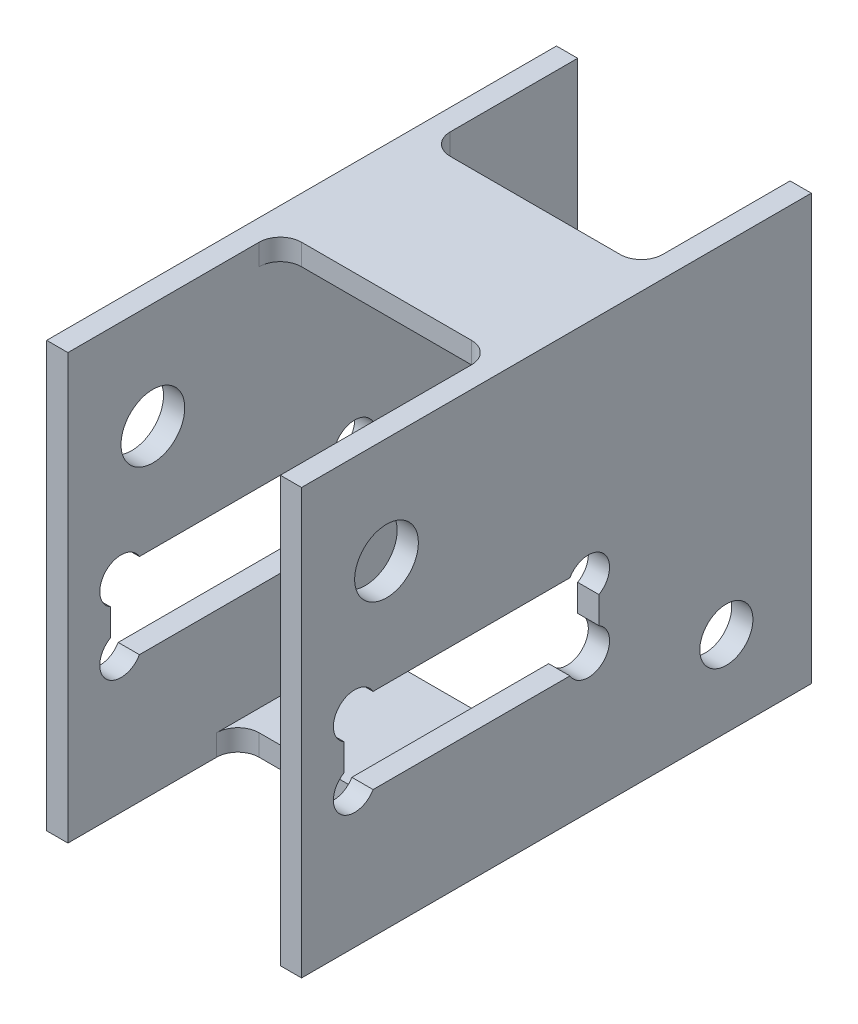
SolidWorks part; units mm, degrees
material "6061 Alloy"
ref_plane "Front Plane" through (0, 0, 0) normal (0, 0, 1) x (1, 0, 0)
ref_plane "Top Plane" through (0, 0, 0) normal (0, 1, 0) x (1, 0, 0)
ref_plane "Right Plane" through (0, 0, 0) normal (1, 0, 0) x (0, 0, -1)
sketch "Sketch1" plane through (0, 0, 0) normal (0, 0, 1) x (1, 0, 0)
  line L1 (-19.05, -31.75) -> (19.05, -31.75)
  line L2 (-19.05, -31.75) -> (-19.05, 31.75)
  line L3 (-19.05, 31.75) -> (19.05, 31.75)
  line L4 (19.05, -31.75) -> (19.05, 31.75)
  line L5 (-19.05, -31.75) -> (19.05, 31.75) construction
  line L6 (-19.05, 31.75) -> (19.05, -31.75) construction
  line L7 (-15.875, -28.575) -> (15.875, -28.575)
  line L8 (-15.875, -28.575) -> (-15.875, 28.575)
  line L9 (-15.875, 28.575) -> (15.875, 28.575)
  line L10 (15.875, -28.575) -> (15.875, 28.575)
  line L11 (-15.875, -28.575) -> (15.875, 28.575) construction
  line L12 (-15.875, 28.575) -> (15.875, -28.575) construction
  point P0 (0, 0)
  point P6 (0, 0)
  dimension "D1" = 63.5
  dimension "D2" = 38.1
  dimension "D3" = 3.175
  dimension "D4" = 3.175
extrude "Boss-Extrude1" add sketch "Sketch1" along normal blind 76.2
sketch "Sketch2" plane through (19.05, 0, 0) normal (1, 0, 0) x (0, 0, -1)
  line L0 (-76.2, -31.75) -> (-76.2, 31.75) construction
  line L1 (-76.2, 31.75) -> (0, 31.75) construction
  line L2 (-50.8, -4.0293) -> (-50.8, -9.0888) construction
  line L3 (-69.85, -12.7) -> (-31.75, -12.7)
  line L4 (-69.85, -12.7) -> (-69.85, 0)
  line L5 (-69.85, 0) -> (-31.75, 0)
  line L6 (-31.75, -12.7) -> (-31.75, 0)
  line L7 (-69.85, -12.7) -> (-31.75, 0) construction
  line L8 (-69.85, 0) -> (-31.75, -12.7) construction
  circle A0 centre (-63.5, 15.875) radius 4.7625
  circle A1 centre (-12.7, -19.05) radius 3.9688
  circle A3 centre (-68.2625, -1.5875) radius 3.175
  circle A4 centre (-68.2625, -11.1125) radius 3.175
  circle A5 centre (-33.3375, -11.1125) radius 3.175
  circle A6 centre (-33.3375, -1.5875) radius 3.175
  point P6 (-50.8, -6.35)
  dimension "D1" = 9.525
  dimension "D10" = 7.9375
  dimension "D11" = 6.35
  dimension "D12" = 1.5875
  dimension "D2" = 12.7
  dimension "D3" = 15.875
  dimension "D4" = 38.1
  dimension "D5" = 12.7
  dimension "D6" = 6.35
  dimension "D7" = 15.875
  dimension "D8" = 50.8
  dimension "D9" = 34.925
  dimension "D13" = 1.5875
  dimension "D14" = 1.5875
extrude "Cut-Extrude1" cut sketch "Sketch2" against normal through all contours L6 A6 L5 A3 L4 A4 L3 A5 | L4 A3 L5 | L5 A3 L4 | A6 L6 L5 | A6 L5 L6 | A5 L6 L3 | A5 L3 L6 | L3 A4 L4 | L4 A4 L3 | A0 | A1
sketch "Sketch3" plane through (0, 31.75, 0) normal (0, 1, 0) x (1, 0, 0)
  line L0 (19.05, -76.2) -> (-19.05, -76.2) construction
  line L1 (-15.875, -44.45) -> (15.875, -44.45)
  line L2 (-15.875, -44.45) -> (-15.875, -76.2)
  line L3 (-15.875, -76.2) -> (15.875, -76.2)
  line L4 (15.875, -44.45) -> (15.875, -76.2)
  line L5 (-15.875, -44.45) -> (15.875, -76.2) construction
  line L6 (-15.875, -76.2) -> (15.875, -44.45) construction
  line L7 (19.05, 0) -> (-19.05, 0) construction
  line L8 (-15.875, -22.225) -> (15.875, -22.225)
  line L9 (-15.875, -22.225) -> (-15.875, 0)
  line L10 (-15.875, 0) -> (15.875, 0)
  line L11 (15.875, -22.225) -> (15.875, 0)
  line L12 (-15.875, -22.225) -> (15.875, 0) construction
  line L13 (-15.875, 0) -> (15.875, -22.225) construction
  line L14 (19.05, -76.2) -> (19.05, 0) construction
  point P0 (0, -60.325)
  point P7 (0, -11.1125)
  dimension "D1" = 3.175
  dimension "D2" = 31.75
  dimension "D3" = 22.225
extrude "Cut-Extrude2" cut sketch "Sketch3" against normal up to next
sketch "Sketch4" plane through (0, -31.75, 0) normal (0, -1, 0) x (1, 0, 0)
  line L0 (-19.05, 0) -> (19.05, 0) construction
  line L1 (-15.875, 31.75) -> (15.875, 31.75)
  line L2 (-15.875, 31.75) -> (-15.875, 0)
  line L3 (-15.875, 0) -> (15.875, 0)
  line L4 (15.875, 31.75) -> (15.875, 0)
  line L5 (-15.875, 31.75) -> (15.875, 0) construction
  line L6 (-15.875, 0) -> (15.875, 31.75) construction
  line L7 (-19.05, 76.2) -> (19.05, 76.2) construction
  line L8 (-15.875, 50.8) -> (15.875, 50.8)
  line L9 (-15.875, 50.8) -> (-15.875, 76.2)
  line L10 (-15.875, 76.2) -> (15.875, 76.2)
  line L11 (15.875, 50.8) -> (15.875, 76.2)
  line L12 (-15.875, 50.8) -> (15.875, 76.2) construction
  line L13 (-15.875, 76.2) -> (15.875, 50.8) construction
  line L14 (19.05, 76.2) -> (19.05, 0) construction
  line L15 (-19.05, 76.2) -> (-19.05, 0) construction
  point P0 (0, 15.875)
  point P7 (0, 63.5)
  dimension "D1" = 31.75
  dimension "D2" = 25.4
  dimension "D3" = 3.175
  dimension "D4" = 3.175
extrude "Cut-Extrude3" cut sketch "Sketch4" against normal up to next
fillet "Fillet1" radius 3.175 8 edges at (15.875, 30.1625, 44.45) (-15.875, 30.1625, 44.45) (15.875, 30.1625, 22.225) (-15.875, 30.1625, 22.225) (-15.875, -30.1625, 31.75) (15.875, -30.1625, 31.75) (15.875, -30.1625, 50.8) (-15.875, -30.1625, 50.8)
